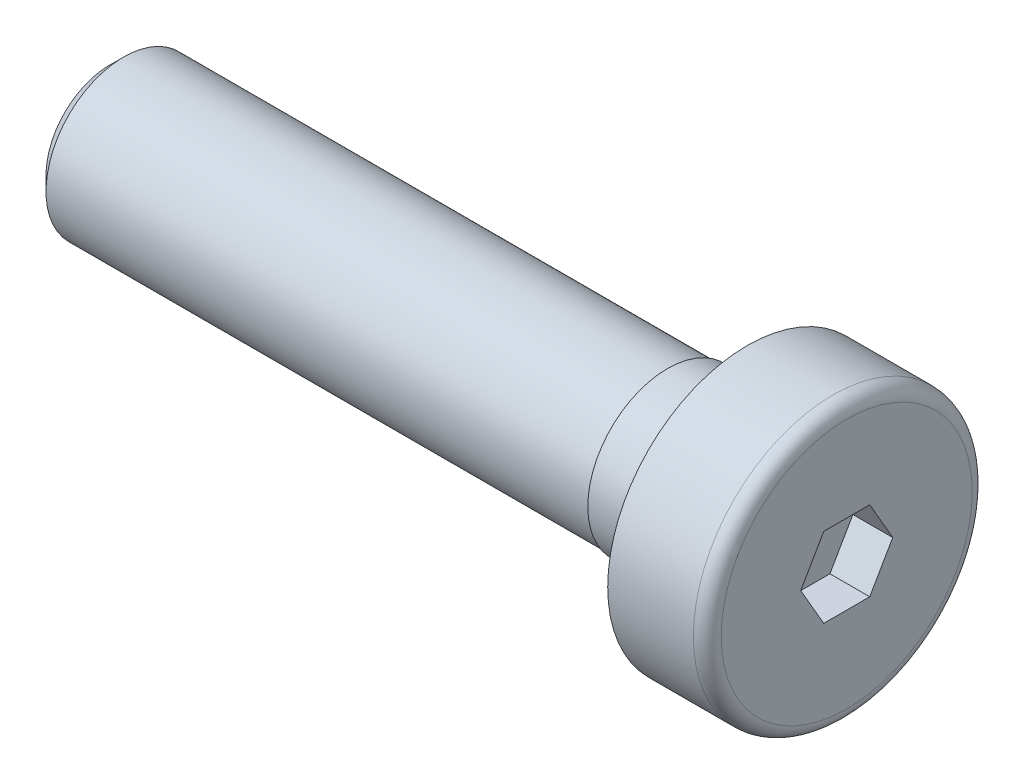
SolidWorks part; units mm, degrees
material "1.0503 (C45)"
ref_plane "Płaszczyzna XY" through (0, 0, 0) normal (0, 0, 1) x (1, 0, 0)
ref_plane "Płaszczyzna XZ" through (0, 0, 0) normal (0, 1, 0) x (1, 0, 0)
ref_plane "Płaszczyzna YZ" through (0, 0, 0) normal (1, 0, 0) x (0, 0, -1)
sketch "Szkic1" plane through (0, 0, 0) normal (0, 0, 1) x (1, 0, 0)
  line L0 (-123.1589, 0) -> (95.9851, 0) construction
  line L1 (0, 0) -> (0, 3.5)
  line L2 (0, 3.5) -> (-2.5, 3.5)
  line L3 (-2.5, 3.5) -> (-2.5, 2)
  line L4 (-2.5, 2) -> (-18.5, 2)
  line L5 (-18.5, 2) -> (-18.5, 0)
  line L6 (0, 0) -> (-18.5, 0)
  dimension "Dk" = 7
  dimension "d" = 4
  dimension "l" = 16
  dimension "k" = 2.5
revolve "Obrót1" add sketch "Szkic1" angle 360 about L0
sketch "Szkic4" plane through (0, 0, 0) normal (0, 1, 0) x (1, 0, 0)
  line L0 (-18.5, -2) -> (-2.5, -2) construction
  line L1 (-4.5, -2) -> (-18.5, -2)
  line L2 (-4.5, -2) -> (-4.5, -1.95)
  line L3 (-4.5, -1.95) -> (-18.5, -1.95)
  line L4 (-18.5, -2) -> (-18.5, -1.95)
  line L5 (-18.5, 2) -> (-18.5, -2) construction
  line L6 (0, 0) -> (-71.6948, 0) construction
  dimension "b" = 14
  dimension "D2" = 0.05
revolve "Wycięcie-obrót1" cut sketch "Szkic4" angle 360 about L6
chamfer "Sfazowanie1" distance 0.35 1 edges at (-18.5, 0, -1.95)
fillet "Zaokrąglenie1" radius 0.35 1 edges at (0, 0, 3.5)
sketch "Szkic2" plane through (0, 0, 0) normal (1, 0, 0) x (0, 0, -1)
  line L1 (1.1547, 0) -> (0.5774, 1)
  line L2 (0.5774, 1) -> (-0.5774, 1)
  line L3 (-0.5774, 1) -> (-1.1547, 0)
  line L4 (-1.1547, 0) -> (-0.5774, -1)
  line L5 (-0.5774, -1) -> (0.5774, -1)
  line L6 (0.5774, -1) -> (1.1547, 0)
  circle A0 centre (0, 0) radius 1 construction
  dimension "s" = 2
extrude "Wytnij-wyciągnięcie1" cut sketch "Szkic2" against normal offset from surface (1 mm away) 1.5 up to face at (-2.5, 0, 2)
